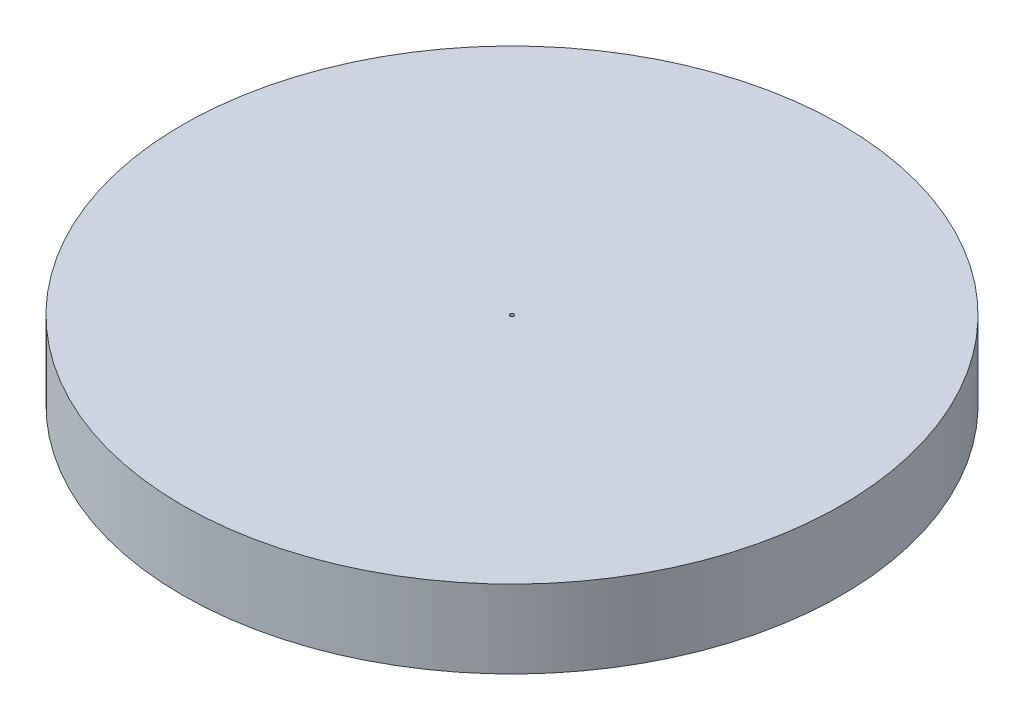
SolidWorks part; units mm, degrees
ref_plane "Front Plane" through (0, 0, 0) normal (0, 0, 1) x (1, 0, 0)
ref_plane "Top Plane" through (0, 0, 0) normal (0, 1, 0) x (1, 0, 0)
ref_plane "Right Plane" through (0, 0, 0) normal (1, 0, 0) x (0, 0, -1)
sketch "Sketch1" plane through (0, 0, 0) normal (0, 1, 0) x (1, 0, 0)
  circle A0 centre (0, 0) radius 12.7
  circle A1 centre (0, 0) radius 0.075
extrude "Boss-Extrude1" add sketch "Sketch1" along normal blind 3
